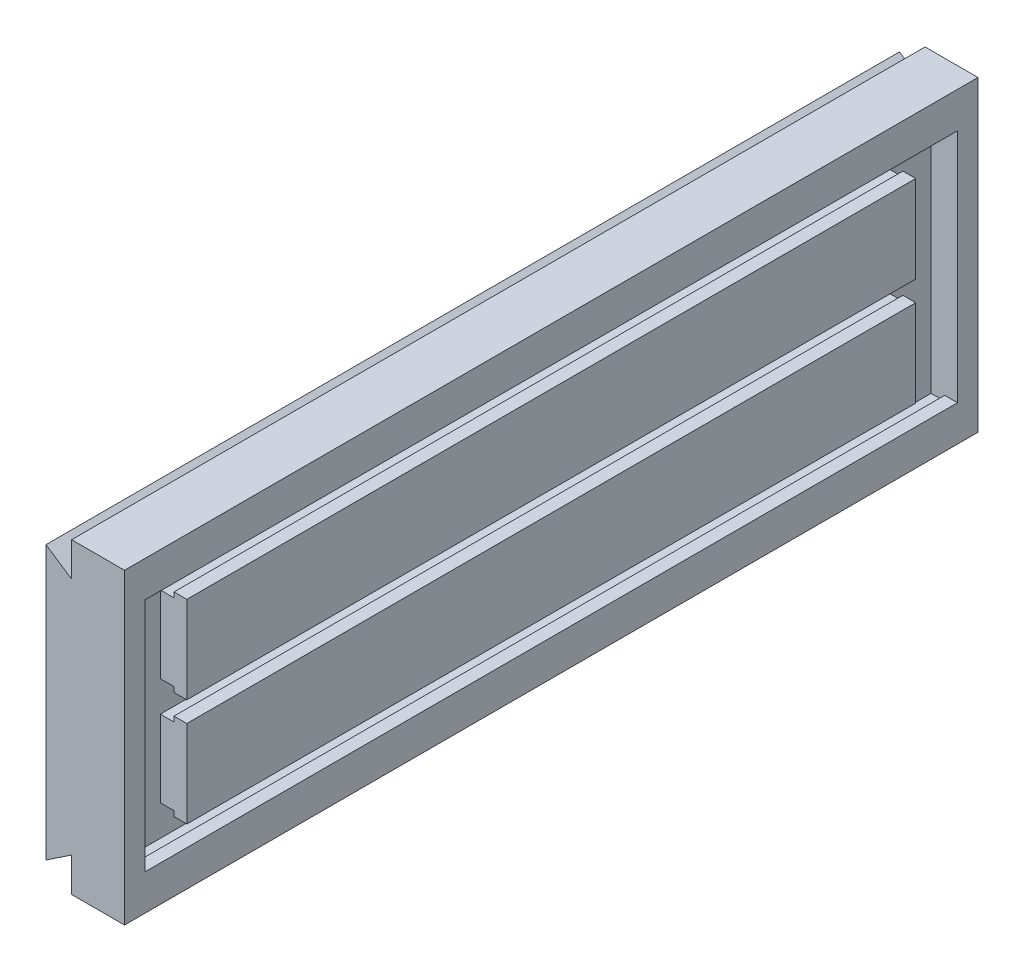
SolidWorks part; units mm, degrees
ref_plane "Front Plane" through (0, 0, 0) normal (0, 0, 1) x (1, 0, 0)
ref_plane "Top Plane" through (0, 0, 0) normal (0, 1, 0) x (1, 0, 0)
ref_plane "Right Plane" through (0, 0, 0) normal (1, 0, 0) x (0, 0, -1)
sketch "Sketch1" plane through (0, 0, 0) normal (0, 0, 1) x (1, 0, 0)
  line L1 (-46, 80) -> (-46, -80)
  line L3 (-31, 70) -> (-46, 80)
  line L5 (-31, 90) -> (-31, 70)
  line L7 (-46, -80) -> (-31, -70)
  line L9 (-31, -70) -> (-31, -90)
  line L10 (-31, 90) -> (0, 90)
  line L11 (0, 90) -> (0, -90)
  line L12 (0, -90) -> (-31, -90)
extrude "Boss-Extrude1" add sketch "Sketch1" along normal mid plane 500
sketch "Sketch2" plane through (0, 0, 0) normal (0, 0, 1) x (1, 0, 0)
  line L0 (0, 69) -> (-7.5, 69)
  line L1 (0, -90) -> (0, 90) construction
  line L2 (-7.5, 69) -> (-7.5, 72)
  line L3 (-7.5, 72) -> (-15.5, 72)
  line L4 (-15.5, 72) -> (-15.5, 54)
  line L5 (-15.5, 54) -> (-7.5, 54)
  line L6 (-7.5, 54) -> (-7.5, 57)
  line L7 (-7.5, 57) -> (0, 57)
  line L8 (0, 57) -> (0, 69)
  line L9 (0, 6) -> (-7.5, 6)
  line L10 (-7.5, 6) -> (-7.5, 9)
  line L11 (-7.5, 9) -> (-15.5, 9)
  line L12 (-15.5, 9) -> (-15.5, -9)
  line L13 (-15.5, -9) -> (-7.5, -9)
  line L14 (-7.5, -9) -> (-7.5, -6)
  line L15 (-7.5, -6) -> (0, -6)
  line L16 (0, -6) -> (0, 6)
  line L17 (0, -69) -> (-7.5, -69)
  line L18 (-7.5, -69) -> (-7.5, -72)
  line L19 (-7.5, -72) -> (-15.5, -72)
  line L20 (-15.5, -72) -> (-15.5, -54)
  line L21 (-15.5, -54) -> (-7.5, -54)
  line L22 (-7.5, -54) -> (-7.5, -57)
  line L23 (-7.5, -57) -> (0, -57)
  line L24 (0, -57) -> (0, -69)
  line L25 (-15.5, -63) -> (18.1494, -63) construction
  line L26 (-15.5, 0) -> (15.1416, 0) construction
  line L27 (-15.5, 63) -> (15.1416, 63) construction
  line L28 (0, 90) -> (-31, 90) construction
  line L29 (-31, -90) -> (0, -90) construction
  dimension "D1" = 15.5
  dimension "D2" = 18
  dimension "D3" = 12
  dimension "D4" = 12
  dimension "D5" = 12
  dimension "D6" = 8
  dimension "D7" = 21
  dimension "D8" = 51
  dimension "D9" = 51
  dimension "D10" = 21
extrude "Cut-Extrude1" cut sketch "Sketch2" against normal mid plane 476
sketch "Sketch3" plane through (0, 0, 0) normal (1, 0, 0) x (0, 0, -1)
  line L1 (-238, 69) -> (-213.5, 69)
  line L2 (-213.5, 69) -> (-213.5, -69)
  line L3 (-238, -69) -> (-213.5, -69)
  line L4 (-238, 69) -> (-238, -69)
  line L5 (238, 69) -> (213.5, 69)
  line L7 (238, 69) -> (-238, 69) construction
  line L8 (238, 69) -> (238, -69)
  line L9 (-250, -90) -> (-250, 90) construction
  line L10 (250, -90) -> (250, 90) construction
  line L11 (213.5, 69) -> (213.5, -69)
  line L12 (238, -69) -> (-238, -69) construction
  line L13 (213.5, -69) -> (238, -69)
  dimension "D1" = 12
  dimension "D2" = 12
  dimension "D3" = 24.5
  dimension "D4" = 24.5
extrude "Cut-Extrude2" cut sketch "Sketch3" against normal up to surface (15.5 mm away) up to face at (-15.5, 0, 0)
